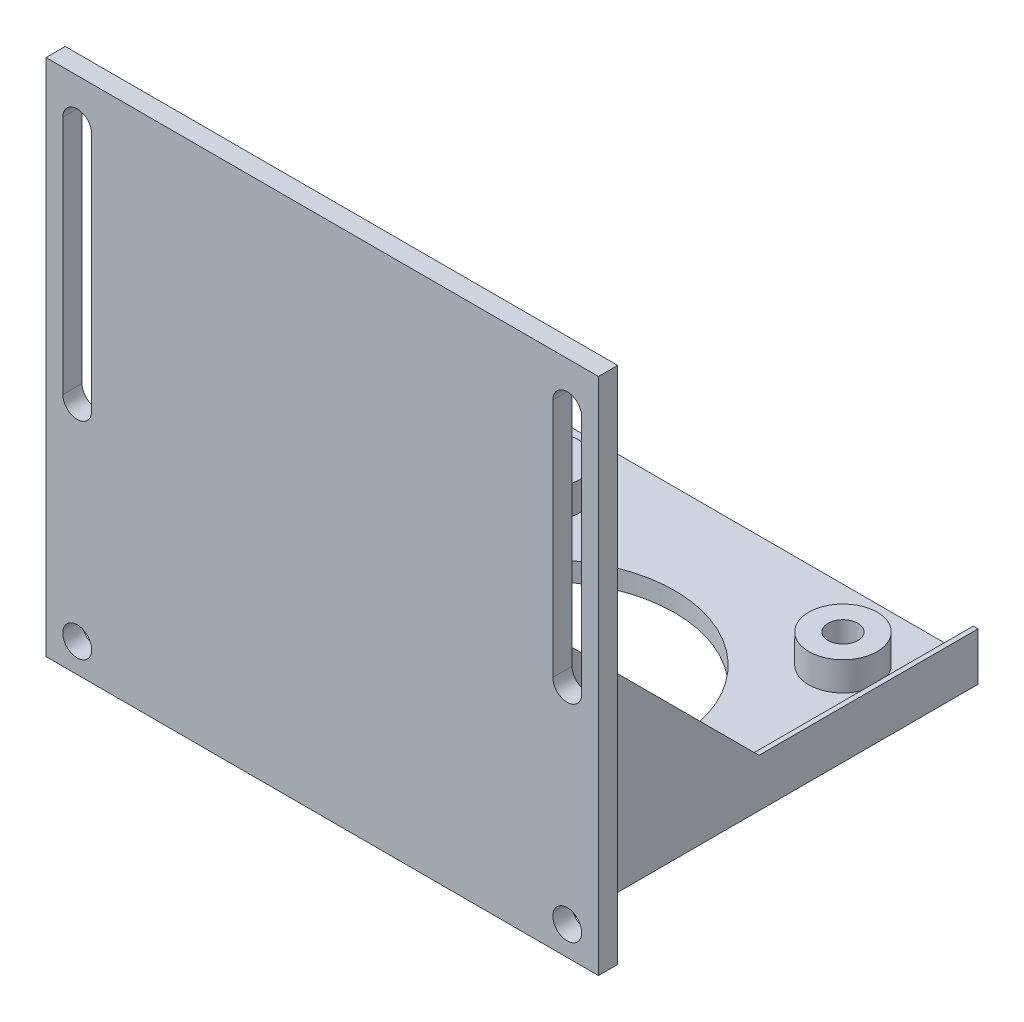
SolidWorks part; units mm, degrees
ref_plane "Front Plane" through (0, 0, 0) normal (0, 0, 1) x (1, 0, 0)
ref_plane "Top Plane" through (0, 0, 0) normal (0, 1, 0) x (1, 0, 0)
ref_plane "Right Plane" through (0, 0, 0) normal (1, 0, 0) x (0, 0, -1)
sketch "Sketch3" plane through (0, 0, 0) normal (0, -1, 0) x (1, 0, 0)
  line L0 (-2.1209, 0) -> (44.5389, 0) construction
  line L1 (22.25, -44) -> (-22.25, -44)
  line L2 (22.25, -44) -> (22.25, 0)
  line L3 (22.25, 0) -> (-22.25, 0)
  line L4 (-22.25, -44) -> (-22.25, 0)
  circle A0 centre (0, -21.209) radius 13.462 construction
  circle A1 centre (15.494, -5.715) radius 1.5541 construction
  circle A2 centre (-15.494, -5.715) radius 1.5541 construction
  circle A3 centre (-15.494, -36.703) radius 1.5541 construction
  circle A4 centre (15.494, -36.703) radius 1.5541 construction
  circle A5 centre (0, -21.209) radius 13.462
  circle A6 centre (15.494, -5.715) radius 1.5541
  circle A7 centre (-15.494, -5.715) radius 1.5541
  circle A8 centre (-15.494, -36.703) radius 1.5541
  circle A9 centre (15.494, -36.703) radius 1.5541
  point P21 (0, -44)
  dimension "D1" = 44.5
  dimension "D2" = 44
extrude "Front Face" add sketch "Sketch3" along normal blind 5
sketch "Sketch4" plane through (0, 0, 0) normal (0, 0, 1) x (1, 0, 0)
  line L0 (-22.25, -5) -> (-22.25, 0) construction
  line L1 (22.25, -5) -> (-22.25, -5)
  line L2 (22.25, -5) -> (22.25, 49)
  line L3 (22.25, 49) -> (-22.25, 49)
  line L4 (-22.25, -5) -> (-22.25, 49)
  dimension "D1" = 54
extrude "Bottom Plate" add sketch "Sketch4" along normal blind 2
sketch "Sketch5" plane through (-22.25, 0, 0) normal (-1, 0, 0) x (0, 0, 1)
  line L0 (-21.209, 0) -> (0, 21.209)
  line L1 (-34.671, 0) -> (-7.747, 0) construction
  line L2 (0, 70.7799) -> (0, 24.1201) construction
  line L3 (0, 7.5692) -> (0, 0.508) construction
  line L4 (-21.209, 0) -> (0, 0)
  line L5 (0, 0) -> (0, 21.209)
  dimension "D1" = 45
extrude "Rib" add sketch "Sketch5" against normal blind 0.5
sketch "Sketch6" plane through (21.209, 47.45, 0) normal (0, 0, -1) x (-1, 0, 0)
  line L1 (43.459, -52.45) -> (49.959, -52.45)
  line L2 (43.459, -52.45) -> (43.459, 1.55)
  line L3 (43.459, 1.55) -> (49.959, 1.55)
  line L4 (49.959, -52.45) -> (49.959, 1.55)
  line L5 (-1.041, 1.55) -> (43.459, 1.55) construction
  line L7 (46.709, -2.95) -> (46.709, -27.95) construction
  line L8 (48.209, -2.95) -> (48.209, -27.95)
  line L9 (45.209, -2.95) -> (45.209, -27.95)
  line L10 (46.709, -52.45) -> (46.709, 1.55) construction
  circle A0 centre (46.709, -49.45) radius 1.5
  arc A1 (48.209, -2.95) -> (45.209, -2.95) centre (46.709, -2.95) ccw
  arc A2 (45.209, -27.95) -> (48.209, -27.95) centre (46.709, -27.95) ccw
  point P10 (46.709, -15.45)
  point P21 (46.709, -1.45)
  dimension "D1" = 3
  dimension "D2" = 3
  dimension "D3" = 25
  dimension "D4" = 3
  dimension "D6" = 6.5
extrude "Bottom Screw Holes" add sketch "Sketch6" against normal up to surface (2 mm away) up to face at (0, 22, 2)
ref_plane "Plane1" through (0, 0, 0) normal (-1, 0, 0) x (0, 0, 1)
mirror "Mirror of Rib and Bottom Screws" about plane through (0, 0, 0) normal (-1, 0, 0) of "Rib", "Bottom Screw Holes", "Front Face", "Bottom Plate"
sketch "Sketch7" plane through (0, 0, -44) normal (0, 0, -1) x (-1, 0, 0)
  line L1 (21.75, 0) -> (-21.75, 0)
  line L2 (21.75, 0) -> (21.75, -3)
  line L3 (21.75, -3) -> (-21.75, -3)
  line L4 (-21.75, 0) -> (-21.75, -3)
  line L7 (-21.75, 21.209) -> (-21.75, 0) construction
  line L8 (21.75, 0) -> (21.75, 21.209) construction
  dimension "D1" = 3
extrude "Cut-Extrude1" cut sketch "Sketch7" against normal up to surface (44 mm away) up to face at (-27, -2, 0)
sketch "Sketch8" plane through (0, -3, 0) normal (0, 1, 0) x (1, 0, 0)
  circle A0 centre (-15.494, 36.703) radius 1.5541 construction
  circle A1 centre (15.494, 36.703) radius 1.5541 construction
  circle A2 centre (-15.494, 36.703) radius 3.5541
  circle A3 centre (15.494, 5.715) radius 1.5541 construction
  circle A4 centre (15.494, 36.703) radius 3.5541
  circle A5 centre (15.494, 5.715) radius 3.5541
  circle A6 centre (-15.494, 5.715) radius 1.5541 construction
  circle A7 centre (-15.494, 5.715) radius 3.5541
  circle A18 centre (-15.494, 5.715) radius 1.5541
  circle A19 centre (15.494, 5.715) radius 1.5541
  circle A20 centre (15.494, 36.703) radius 1.5541
  circle A21 centre (-15.494, 36.703) radius 1.5541
  dimension "D1" = 2
extrude "Boss-Extrude5" add sketch "Sketch8" along normal blind 3
